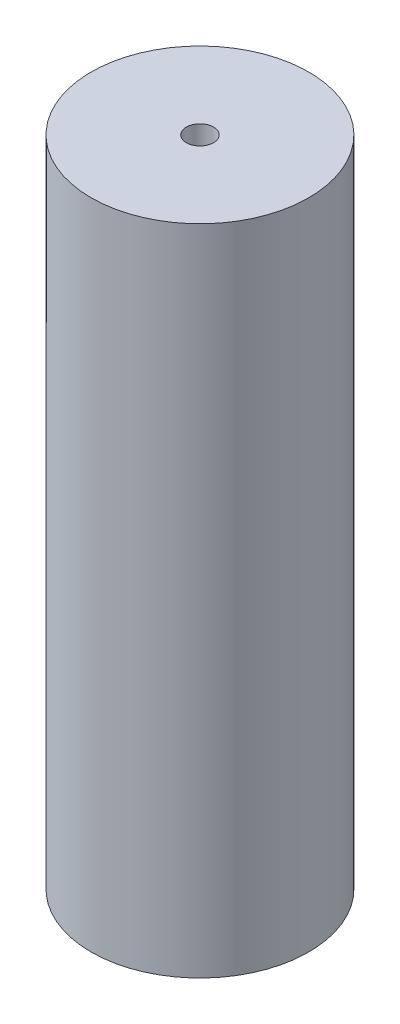
SolidWorks part; units mm, degrees
ref_plane "Front Plane" through (0, 0, 0) normal (0, 0, 1) x (1, 0, 0)
ref_plane "Top Plane" through (0, 0, 0) normal (0, 1, 0) x (1, 0, 0)
ref_plane "Right Plane" through (0, 0, 0) normal (1, 0, 0) x (0, 0, -1)
sketch "Sketch1" plane through (0, 0, 0) normal (0, 1, 0) x (1, 0, 0)
  circle A0 centre (0, 0) radius 25.4
  dimension "D1" = 50.8
extrude "Boss-Extrude1" add sketch "Sketch1" along normal blind 152.4
sketch "Sketch4" plane through (0, 0, 0) normal (0, -1, 0) x (1, 0, 0)
  circle A0 centre (0, 0) radius 3.175
  dimension "D1" = 6.35
extrude "Cut-Extrude1" cut sketch "Sketch4" against normal blind 152.4 contours A0
